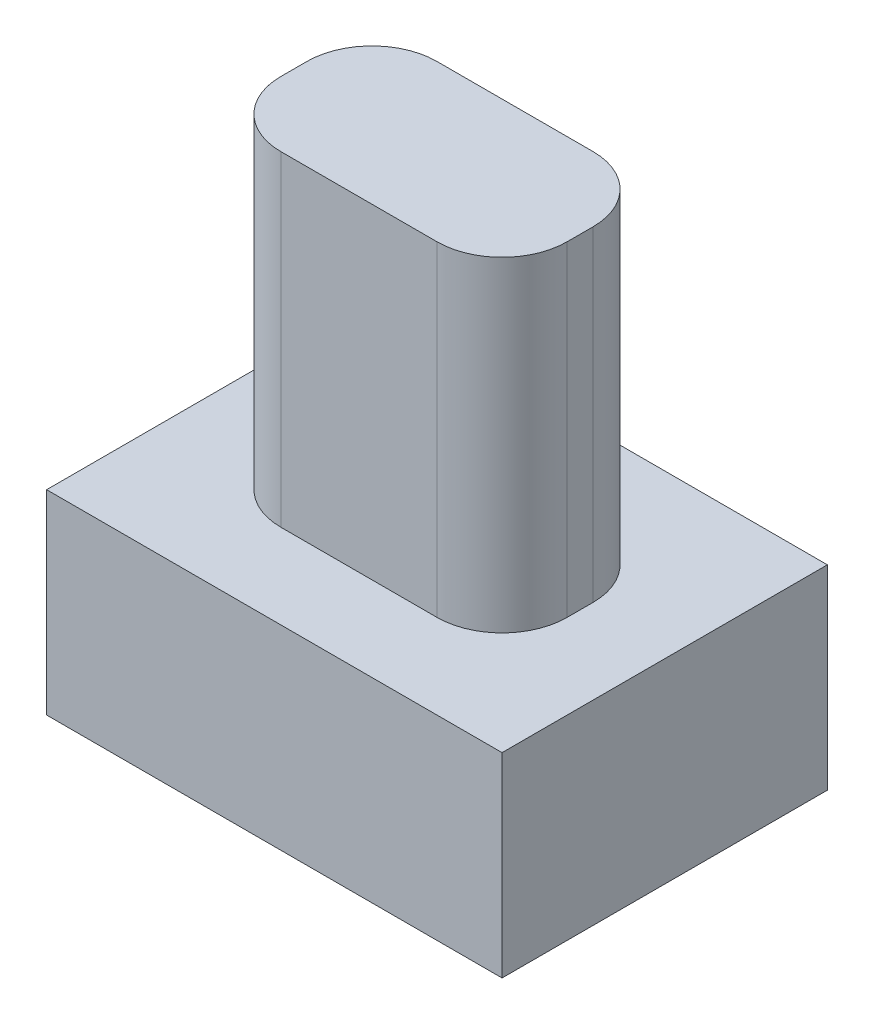
SolidWorks part; units mm, degrees
ref_plane "Front Plane" through (0, 0, 0) normal (0, 0, 1) x (1, 0, 0)
ref_plane "Top Plane" through (0, 0, 0) normal (0, 1, 0) x (1, 0, 0)
ref_plane "Right Plane" through (0, 0, 0) normal (1, 0, 0) x (0, 0, -1)
sketch "Sketch1" plane through (0, 0, 0) normal (0, 1, 0) x (1, 0, 0)
  line L1 (-3.5, 2.5) -> (3.5, 2.5)
  line L2 (-3.5, 2.5) -> (-3.5, -2.5)
  line L3 (-3.5, -2.5) -> (3.5, -2.5)
  line L4 (3.5, 2.5) -> (3.5, -2.5)
  line L5 (-3.5, 2.5) -> (3.5, -2.5) construction
  line L6 (-3.5, -2.5) -> (3.5, 2.5) construction
  point P0 (0, 0)
  dimension "D1" = 5
  dimension "D2" = 7
extrude "Boss-Extrude1" add sketch "Sketch1" along normal blind 3
sketch "Sketch2" plane through (0, 3, 0) normal (0, 1, 0) x (1, 0, 0)
  line L1 (-2.2, 1.2) -> (2.2, 1.2)
  line L2 (-2.2, 1.2) -> (-2.2, -1.2)
  line L3 (-2.2, -1.2) -> (2.2, -1.2)
  line L4 (2.2, 1.2) -> (2.2, -1.2)
  line L5 (-2.2, 1.2) -> (2.2, -1.2) construction
  line L6 (-2.2, -1.2) -> (2.2, 1.2) construction
  point P0 (0, 0)
  dimension "D1" = 2.4
  dimension "D2" = 4.4
extrude "Boss-Extrude2" add sketch "Sketch2" along normal blind 5
fillet "Fillet1" radius 1 4 edges at (-2.2, 5.5, -1.2) (2.2, 5.5, -1.2) (2.2, 5.5, 1.2) (-2.2, 5.5, 1.2)
